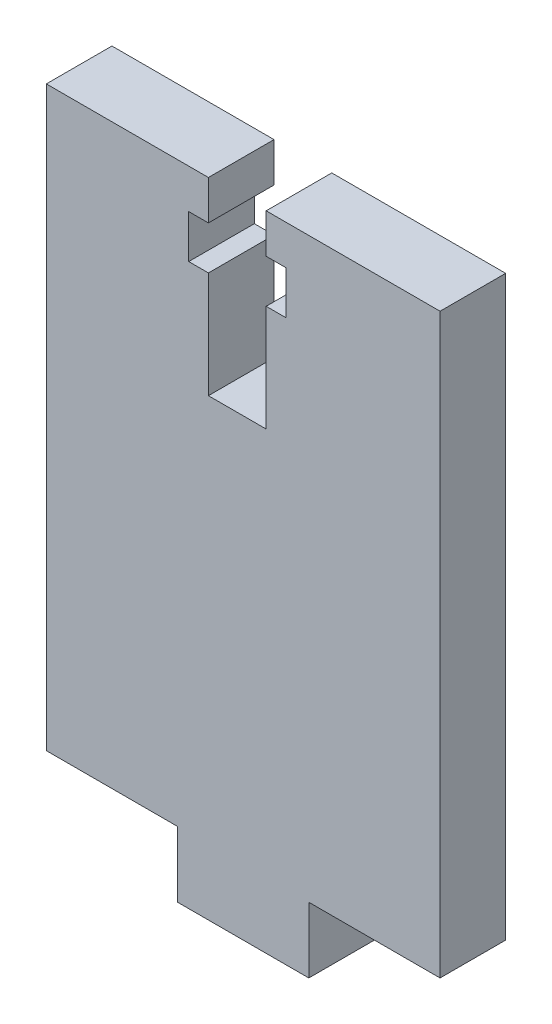
SolidWorks part; units mm, degrees
ref_plane "Front Plane" through (0, 0, 0) normal (0, 0, 1) x (1, 0, 0)
ref_plane "Top Plane" through (0, 0, 0) normal (0, 1, 0) x (1, 0, 0)
ref_plane "Right Plane" through (0, 0, 0) normal (1, 0, 0) x (0, 0, -1)
sketch "Sketch1" plane through (0, 0, 0) normal (0, 0, 1) x (1, 0, 0)
  line L0 (-5.2768, 0) -> (4.7232, 0)
  line L1 (4.7232, 0) -> (4.7232, 5)
  line L2 (4.7232, 5) -> (14.7232, 5)
  line L3 (14.7232, 5) -> (14.7232, 49)
  line L4 (14.7232, 49) -> (-15.2768, 49)
  line L5 (-15.2768, 49) -> (-15.2768, 5)
  line L6 (-15.2768, 5) -> (-5.2768, 5)
  line L7 (-5.2768, 5) -> (-5.2768, 0)
  dimension "D1" = 10
  dimension "D2" = 5
  dimension "D3" = 5
  dimension "D4" = 10
  dimension "D5" = 10
  dimension "D6" = 44
extrude "Boss-Extrude1" add sketch "Sketch1" along normal blind 5
sketch "Sketch2" plane through (0, 0, 0) normal (0, 0, -1) x (-1, 0, 0)
  line L0 (-1.4729, 34.6) -> (2.9271, 34.6)
  line L1 (2.9271, 42.7) -> (2.9271, 34.6)
  line L2 (4.4271, 42.7) -> (2.9271, 42.7)
  line L3 (4.4271, 46) -> (4.4271, 42.7)
  line L4 (2.9271, 46) -> (4.4271, 46)
  line L5 (2.9271, 49) -> (2.9271, 46)
  line L6 (-1.4729, 49) -> (2.9271, 49)
  line L7 (-1.4729, 46) -> (-1.4729, 49)
  line L8 (-2.9729, 46) -> (-1.4729, 46)
  line L9 (-2.9729, 42.7) -> (-2.9729, 46)
  line L10 (-1.4729, 42.7) -> (-2.9729, 42.7)
  line L11 (-1.4729, 34.6) -> (-1.4729, 42.7)
  line L13 (-14.7232, 49) -> (15.2768, 49) construction
  line L14 (-14.7232, 5) -> (-14.7232, 49) construction
  dimension "D1" = 4.4
  dimension "D2" = 3
  dimension "D3" = 13.2504
  dimension "D4" = 1.5
  dimension "D5" = 1.5
  dimension "D6" = 3.3
extrude "Cut-Extrude1" cut sketch "Sketch2" against normal blind 5
